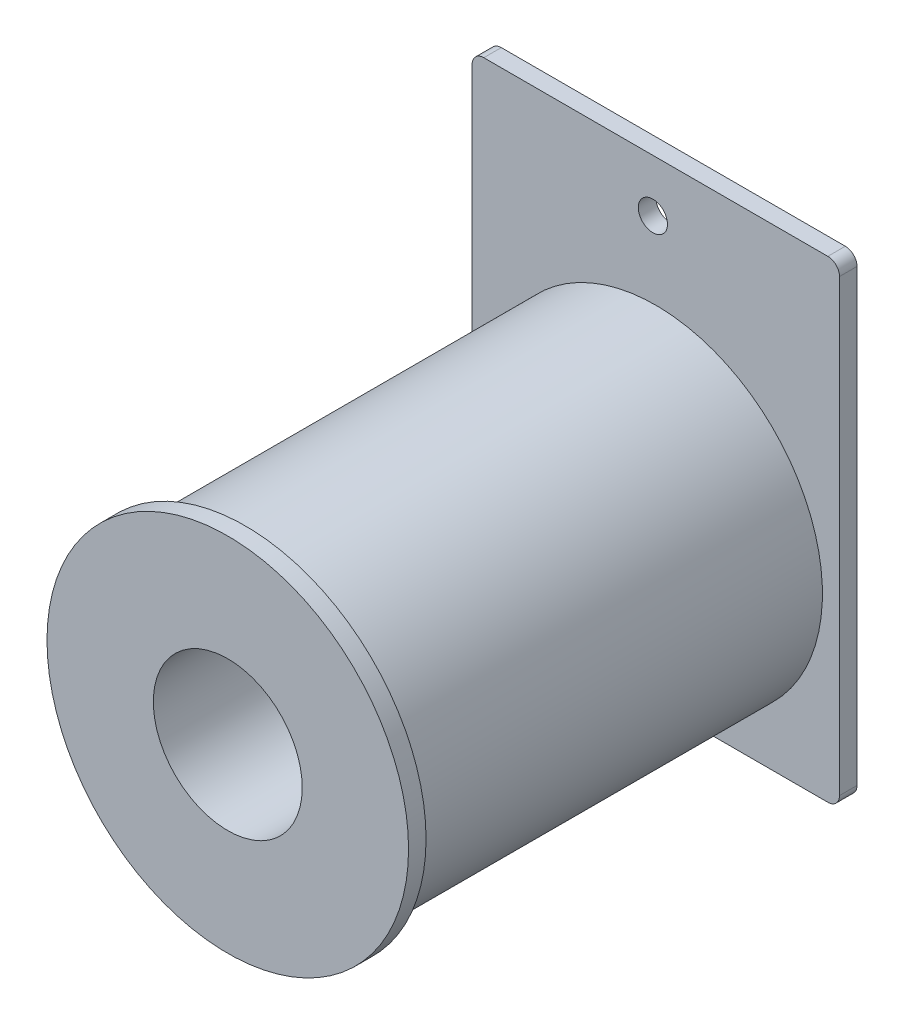
SolidWorks part; units mm, degrees
material "ABS"
ref_plane "Plan de face" through (0, 0, 0) normal (0, 0, 1) x (1, 0, 0)
ref_plane "Plan de dessus" through (0, 0, 0) normal (0, 1, 0) x (1, 0, 0)
ref_plane "Plan de droite" through (0, 0, 0) normal (1, 0, 0) x (0, 0, -1)
sketch "Esquisse1" plane through (0, 0, 0) normal (0, 0, 1) x (1, 0, 0)
  circle A0 centre (0, 0) radius 14.285
  dimension "D1" = 28.57
extrude "Boss.-Extru.1" add sketch "Esquisse1" along normal blind 35.2
sketch "Esquisse2" plane through (0, 0, 35.2) normal (0, 0, 1) x (1, 0, 0)
  circle A0 centre (0, 0) radius 15.5
  dimension "D1" = 31
extrude "Boss.-Extru.2" add sketch "Esquisse2" along normal blind 1.5
sketch "Esquisse4" plane through (0, 0, 0) normal (0, 0, -1) x (-1, 0, 0)
  line L0 (0, 14.285) -> (0, 25.285) construction
  line L1 (-14.75, 25.285) -> (14.75, 25.285)
  line L2 (-15.75, 24.285) -> (-15.75, -14.255)
  line L3 (-14.75, -15.255) -> (14.75, -15.255)
  line L4 (15.75, 24.285) -> (15.75, -14.255)
  circle A2 centre (0, 0) radius 14.285 construction
  circle A3 centre (0, 0) radius 14.285 construction
  arc A4 (14.75, -15.255) -> (15.75, -14.255) centre (14.75, -14.255) ccw
  arc A5 (-15.75, -14.255) -> (-14.75, -15.255) centre (-14.75, -14.255) ccw
  arc A6 (15.75, 24.285) -> (14.75, 25.285) centre (14.75, 24.285) ccw
  arc A7 (-14.75, 25.285) -> (-15.75, 24.285) centre (-14.75, 24.285) ccw
  point P13 (15.75, -15.255)
  point P16 (-15.75, -15.255)
  dimension "D2" = 31.5
  dimension "D5" = 1
  dimension "D1" = 40.54
  dimension "D3" = 15.75
  dimension "D4" = 11
extrude "Boss.-Extru.3" add sketch "Esquisse4" along normal blind 1.5 contours L1 A6 L4 A4 L3 A5 L2 A7
sketch "Esquisse3" plane through (0, 0, 36.7) normal (0, 0, 1) x (1, 0, 0)
  line L0 (-15.75, 24.285) -> (-15.75, -14.255) construction
  line L1 (14.75, 25.285) -> (-14.75, 25.285) construction
  circle A0 centre (0, 0) radius 6.385
  circle A1 centre (-0.25, 20.785) radius 1.25
  dimension "D1" = 12.77
  dimension "D4" = 2.5
  dimension "D2" = 15.5
  dimension "D3" = 4.5
extrude "Enlèv. mat.-Extru.1" cut sketch "Esquisse3" against normal through all
